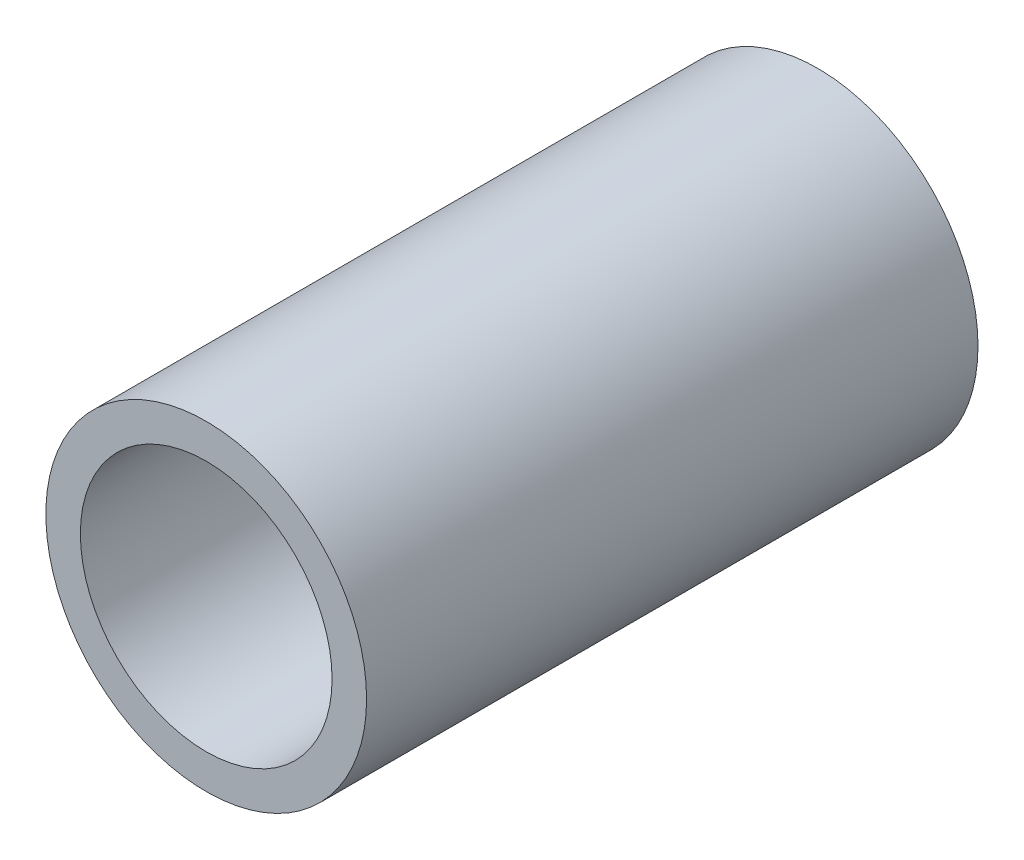
SolidWorks part; units mm, degrees
material "PVC 0.007 Plasticized"
ref_plane "Front Plane" through (0, 0, 0) normal (0, 0, 1) x (1, 0, 0)
ref_plane "Top Plane" through (0, 0, 0) normal (0, 1, 0) x (1, 0, 0)
ref_plane "Right Plane" through (0, 0, 0) normal (1, 0, 0) x (0, 0, -1)
sketch "Sketch1" plane through (0, 0, 0) normal (0, 0, 1) x (1, 0, 0)
  line L0 (10.4648, 0) -> (13.335, 0) construction
  circle A0 centre (0, 0) radius 13.335 construction
  circle A1 centre (0, 0) radius 10.4648 construction
  dimension "ID" = 20.9296
  dimension "OD" = 26.67
  dimension "Wall Thickness" = 2.8702
sketch "Sketch2" plane through (0, 0, 0) normal (1, 0, 0) x (0, 0, -1)
  line L0 (-762, 0) -> (762, 0) construction
  line L1 (-728.6625, 13.335) -> (-728.6625, -13.335) construction
  line L2 (728.6625, 13.335) -> (728.6625, -13.335) construction
  point P4 (0, 0)
  point P8 (-728.6625, 0)
  point P11 (728.6625, 0)
  dimension "Length" = 1524
  dimension "D1" = 33.3375
  dimension "D2" = 33.3375
  dimension "D3" = 26.67
sketch "Sketch3" plane through (0, 0, 0) normal (0, 0, 1) x (1, 0, 0)
  circle A0 centre (0, 0) radius 13.335
  circle A1 centre (0, 0) radius 13.335 construction
  circle A2 centre (0, 0) radius 10.4648 construction
  circle A3 centre (0, 0) radius 10.4648
extrude "Boss-Extrude1" add sketch "Sketch3" along normal up to vertex (762 mm away) and the other way up to vertex (762 mm away) up to point (0, 0, 762) other way up to point (0, 0, -762)
sketch "Sketch4" plane through (0, 0, 762) normal (0, 0, 1) x (1, 0, 0)
  circle A0 centre (0, 0) radius 10.4648 construction
  circle A1 centre (0, 0) radius 13.335 construction
  circle A2 centre (0, 0) radius 10.4648
  circle A3 centre (0, 0) radius 13.335
extrude "Cut-Extrude2" cut sketch "Sketch4" against normal offset from surface (1473.159 mm away) 50.841 contours A3 up to face at (10.4648, 0, -762)
equation "\"D1@Sketch2\"=\"OD@Sketch1\" * 1.25"
equation "\"D2@Sketch2\"=\"D1@Sketch2\""
equation "\"D3@Sketch2\"= \"OD@Sketch1\""
